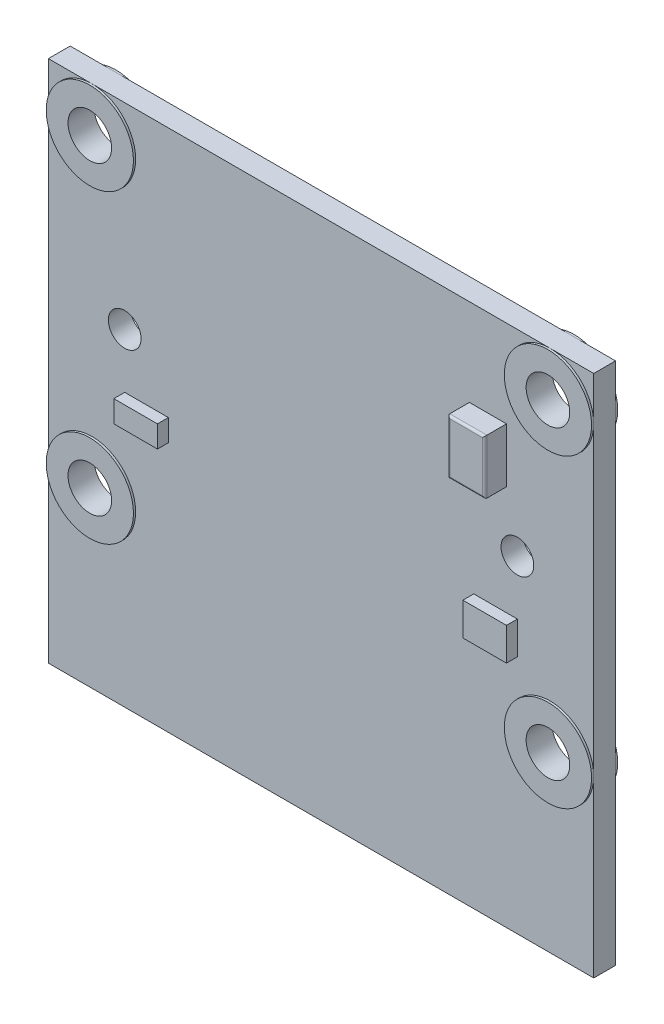
SolidWorks part; units mm, degrees
ref_plane "Front Plane" through (0, 0, 0) normal (0, 0, 1) x (1, 0, 0)
ref_plane "Top Plane" through (0, 0, 0) normal (0, 1, 0) x (1, 0, 0)
ref_plane "Right Plane" through (0, 0, 0) normal (1, 0, 0) x (0, 0, -1)
sketch "Sketch1" plane through (0, 0, 0) normal (0, 0, 1) x (1, 0, 0)
  line L1 (-12.5, 12) -> (12.5, 12)
  line L2 (-12.5, 12) -> (-12.5, -12)
  line L3 (-12.5, -12) -> (12.5, -12)
  line L4 (12.5, 12) -> (12.5, -12)
  line L5 (-12.5, 12) -> (12.5, -12) construction
  line L6 (-12.5, -12) -> (12.5, 12) construction
  point P0 (0, 0)
  dimension "D1" = 25
  dimension "D2" = 24
extrude "Boss-Extrude1" add sketch "Sketch1" along normal blind 1
sketch "Sketch2" plane through (0, 0, 1) normal (0, 0, 1) x (1, 0, 0)
  line L0 (12.5, 12) -> (-12.5, 12) construction
  line L1 (12.5, -12) -> (12.5, 12) construction
  circle A0 centre (-10.5, 10) radius 1
  circle A1 centre (10.5, 10) radius 1
  circle A2 centre (10.5, -4) radius 1
  circle A3 centre (-10.5, -4) radius 1
  circle A4 centre (-9, 3) radius 0.75
  circle A5 centre (9, 3) radius 0.75
  dimension "D9" = 2
  dimension "D10" = 2
  dimension "D11" = 2
  dimension "D12" = 2
  dimension "D13" = 1.5
  dimension "D14" = 1.5
  dimension "D1" = 21
  dimension "D2" = 21
  dimension "D3" = 14
  dimension "D4" = 14
  dimension "D5" = 2
  dimension "D6" = 2
  dimension "D7" = 2
  dimension "D8" = 2
  dimension "D15" = 18
  dimension "D16" = 9
  dimension "D17" = 9
extrude "Cut-Extrude1" cut sketch "Sketch2" against normal blind 2
sketch "Sketch3" plane through (0, 0, 1) normal (0, 0, 1) x (1, 0, 0)
  circle A0 centre (-10.5, 10) radius 2
  circle A1 centre (10.5, 10) radius 2
  circle A2 centre (10.5, -4) radius 2
  circle A3 centre (-10.5, -4) radius 2
  circle A4 centre (-10.5, 10) radius 1
  circle A5 centre (10.5, 10) radius 1
  circle A6 centre (10.5, -4) radius 1
  circle A7 centre (-10.5, -4) radius 1
  circle A8 centre (-10.5, 10) radius 1
  circle A9 centre (10.5, 10) radius 1
  circle A10 centre (10.5, -4) radius 1
  circle A11 centre (-10.5, -4) radius 1
  circle M3 centre (10.5, 10) radius 1
  circle M4 centre (10.5, -4) radius 1
  circle M5 centre (-10.5, -4) radius 1
  circle M8 centre (-10.5, 10) radius 1
  dimension "D1" = 4
  dimension "D2" = 4
  dimension "D3" = 4
  dimension "D4" = 4
  dimension "D5" = 1
extrude "Boss-Extrude3" add sketch "Sketch3" along normal blind 0.1 and the other way blind 1.1 contours A0 M8 | A1 M3 | A2 M4 | A3 M5
sketch "Sketch4" plane through (0, 0, 1) normal (0, 0, 1) x (1, 0, 0)
  line L0 (10.5, 12) -> (-10.5, 12) construction
  line L1 (6.8, 8) -> (8.5, 8)
  line L2 (6.8, 8) -> (6.8, 5.5)
  line L3 (6.8, 5.5) -> (8.5, 5.5)
  line L4 (8.5, 8) -> (8.5, 5.5)
  line L5 (6.8, 8) -> (8.5, 5.5) construction
  line L6 (6.8, 5.5) -> (8.5, 8) construction
  line L7 (12.5, -4) -> (12.5, 10) construction
  point P0 (7.65, 6.75)
  dimension "D1" = 1.7
  dimension "D2" = 2.5
  dimension "D3" = 4
  dimension "D4" = 4
extrude "Boss-Extrude4" add sketch "Sketch4" along normal blind 1
fillet "Fillet1" radius 0.1 4 edges at (7.65, 5.5, 2) (6.8, 6.75, 2) (7.65, 8, 2) (8.5, 6.75, 2)
sketch "Sketch5" plane through (0, 0, 1) normal (0, 0, 1) x (1, 0, 0)
  line L0 (12.5, -4) -> (12.5, 10) construction
  line L1 (-9, 0.5) -> (-7, 0.5)
  line L2 (-9, 0.5) -> (-9, -0.5)
  line L3 (-9, -0.5) -> (-7, -0.5)
  line L4 (-7, 0.5) -> (-7, -0.5)
  line L5 (-9, 0.5) -> (-7, -0.5) construction
  line L6 (-9, -0.5) -> (-7, 0.5) construction
  line L7 (7, 0.5) -> (9, 0.5)
  line L8 (7, 0.5) -> (7, -1)
  line L9 (7, -1) -> (9, -1)
  line L10 (9, 0.5) -> (9, -1)
  line L11 (7, 0.5) -> (9, -1) construction
  line L12 (7, -1) -> (9, 0.5) construction
  line L13 (-12.5, -12) -> (12.5, -12) construction
  line L14 (-12.5, 10) -> (-12.5, -4) construction
  point P0 (-8, 0)
  point P5 (8, -0.25)
  dimension "D1" = 2
  dimension "D2" = 1
  dimension "D3" = 2
  dimension "D4" = 1.5
  dimension "D5" = 3.5
  dimension "D6" = 11
  dimension "D7" = 11.5
  dimension "D8" = 3.5
extrude "Boss-Extrude5" add sketch "Sketch5" along normal blind 0.5
